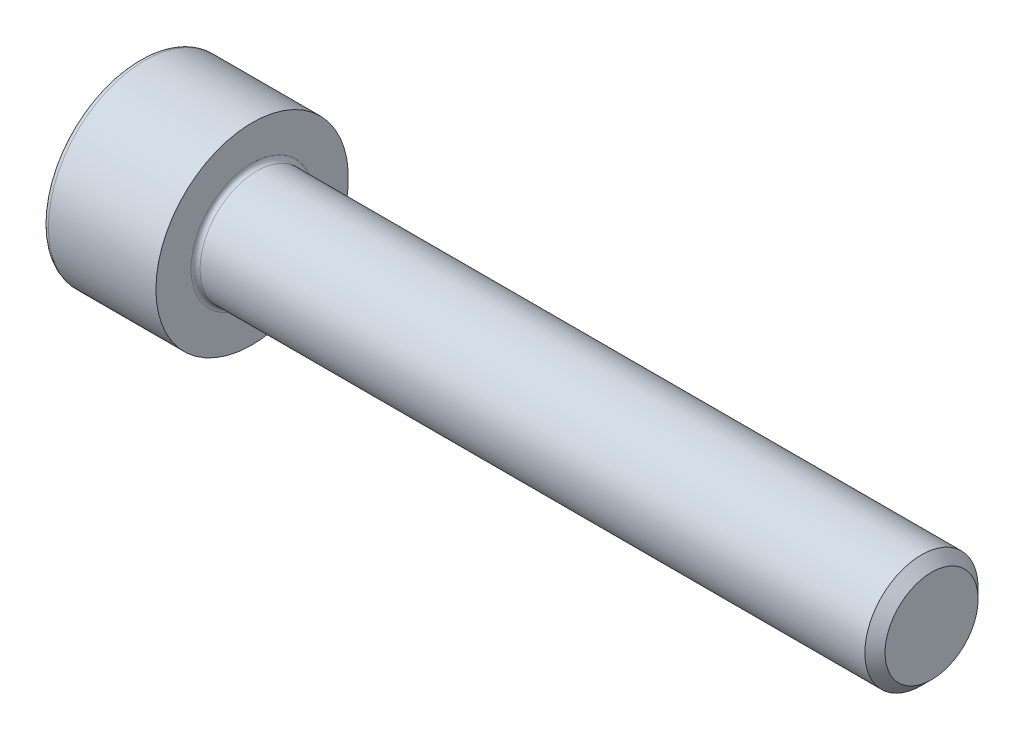
SolidWorks part; units mm, degrees
material "1023 Carbon Steel Sheet (SS)"
ref_plane "Plane1" through (0, 0, 0) normal (0, 0, 1) x (1, 0, 0)
ref_plane "Plane2" through (0, 0, 0) normal (0, 1, 0) x (1, 0, 0)
ref_plane "Plane3" through (0, 0, 0) normal (1, 0, 0) x (0, 0, -1)
sketch "BodySke" plane through (0, 0, 0) normal (0, 0, 1) x (1, 0, 0)
  line L0 (0, 0) -> (0, 4.25)
  line L1 (0, 4.25) -> (5, 4.25)
  line L2 (5, 4.25) -> (5, 2.5)
  line L3 (5, 2.5) -> (34.555, 2.5)
  line L4 (35, 2.055) -> (35, 0)
  line L5 (35, 0) -> (0, 0)
  line L6 (-31.75, 0) -> (127, 0) construction
  line L8 (35, 2.055) -> (34.555, 2.5)
  line L10 (35, -2.055) -> (34.555, -2.5) construction
  line L11 (5.8, 9.525) -> (5.8, 3.175) construction
  line L12 (13, 9.525) -> (13, 3.175) construction
  line L13 (-25, 9.525) -> (-25, 3.175) construction
  dimension "Diameter" = 5
  dimension "Head_ht" = 5
  dimension "Length" = 30
  dimension "Body_ch_ang" = 45
  dimension "Head_dia" = 8.5
  dimension "Minor_dia" = 4.11
  dimension "Advance" = 0.8
  dimension "Thread_nom" = 22
  dimension "Thread_length" = 60
revolve "Base-Revolve" add sketch "BodySke"
cosmetic thread "ThreadCosmetic"
fillet "Fillet1" radius 0.2 1 edges at (5, 0, 2.5)
fillet "Fillet2" radius 0.25 1 edges at (0, 0, 4.25)
sketch "Sketch2" plane through (0, 0, 0) normal (0, 0, 1) x (1, 0, 0)
  line L0 (0, 2.042) -> (2.5, 2.042)
  line L1 (2.5, 2.042) -> (3.6789, 0)
  line L2 (-31.75, 0) -> (127, 0) construction
  line L3 (3.6789, 0) -> (0, 0)
  line L4 (0, 0) -> (0, 2.042)
  line L6 (0, 0) -> (47.625, 0) construction
  dimension "D1" = 2.042
  dimension "D2" = 60
  dimension "Depth" = 2.5
revolve "Hex-PreBroach" cut sketch "Sketch2" angle 360 about L6
sketch "Sketch3" plane through (0, 0, 0) normal (-1, 0, 0) x (0, 0.5, 0.866)
  line L0 (1.1789, 2.042) -> (-1.1789, 2.042)
  line L1 (-1.1789, 2.042) -> (-2.3579, 0)
  line L2 (1.1789, 2.042) -> (2.3579, 0)
  line L3 (1.1789, -2.042) -> (2.3579, 0)
  line L4 (1.1789, -2.042) -> (-1.1789, -2.042)
  line L5 (-1.1789, -2.042) -> (-2.3579, 0)
  dimension "D1" = 2.042
  dimension "D2" = 2.042
  dimension "Hex_size" = 4.084
extrude "Hex" cut sketch "Sketch3" against normal blind 2.5
sketch "ThdSchSke" plane through (0, 0, 0) normal (0, 0, 1) x (1, 0, 0)
  line L0 (13, -2.055) -> (12.6884, -2.5)
  line L1 (13, -2.055) -> (13.3116, -2.5)
  line L2 (13.3116, -2.5) -> (13.3116, -3.125)
  line L3 (-3.175, 0) -> (5.1513, 0) construction
  line L4 (0, 4) -> (0, -4) construction
  line L5 (13.3116, -3.125) -> (12.6884, -3.125)
  line L6 (12.6884, -3.125) -> (12.6884, -2.5)
  dimension "Thread_minor" = 4.11
  dimension "Diameter" = 5
  dimension "Start" = 13
  dimension "SideAngle" = 55
  dimension "VeeAngle" = 70
  dimension "Overcut" = 6.25
revolve "ThreadSchematic" [suppressed] cut sketch "ThdSchSke" angle 360 about L3
pattern_linear "ThdSchPat" [suppressed]
equation "\"D2@Sketch3\" = \"Hex_size@Sketch3\" / 2"
equation "\"D1@Sketch3\" = \"Hex_size@Sketch3\" / 2"
equation "\"D1@Sketch2\" = \"Hex_size@Sketch3\" / 2"
equation "\"Thread_minor@ThreadCosmetic\"  =  \"Minor_dia@BodySke\""
equation "\"Depth@Sketch2\" =  \"Key_eng@Hex\""
equation "\"Thread_length@ThreadCosmetic\" = ((sgn( (\"Length@BodySke\" - \"Advance@BodySke\" * 3.0) - \"Thread_nom@BodySke\" )-1)*( (\"Length@BodySke\" - \"Advance@BodySke\" * 3.0) - \"Thread_nom@BodySke\" ))/-2+ \"Thread_nom@BodySke\""
equation "\"Thread_minor@ThdSchSke\" = \"Minor_dia@BodySke\""
equation "\"Diameter@ThdSchSke\" = \"Diameter@BodySke\""
equation "\"Overcut@ThdSchSke\" = \"Diameter@BodySke\" * 1.25"
equation "\"Start@ThdSchSke\" = \"Head_ht@BodySke\" + \"Length@BodySke\" - \"Thread_length@ThreadCosmetic\"  '---Non-countersunk---"
equation "\"Num_threads@ThdSchPat\" = int( \"Thread_length@ThreadCosmetic\" / \"Advance@BodySke\" + 0.999 )  + 1"
equation "\"Advance@ThdSchPat\" = \"Thread_length@ThreadCosmetic\" /  (\"Num_threads@ThdSchPat\" - 1) 'relax it"
equation "\"Num_threads@ThdSchPat\" = \"Num_threads@ThdSchPat\" - sgn( \"Num_threads@ThdSchPat\" - 1) '---chamfered tips only---"
